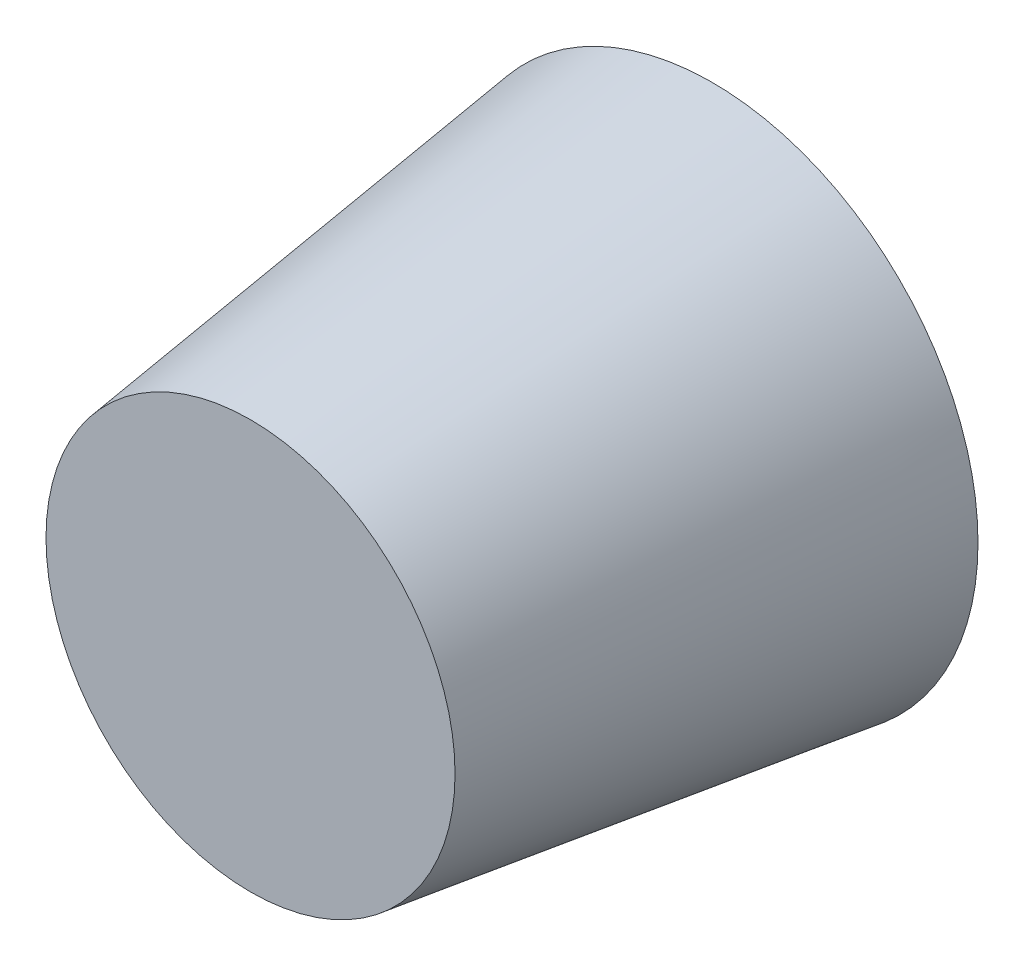
SolidWorks part; units mm, degrees
ref_plane "Front" through (0, 0, 0) normal (0, 0, 1) x (1, 0, 0)
ref_plane "Top" through (0, 0, 0) normal (0, 1, 0) x (1, 0, 0)
ref_plane "Right" through (0, 0, 0) normal (1, 0, 0) x (0, 0, -1)
sketch "草图4" plane through (0, 0, 0) normal (0, 1, 0) x (1, 0, 0)
  line L0 (0, 0) -> (0, 1)
  line L1 (0, 1) -> (14.5, 1)
  line L2 (0, 0) -> (15.5, 0)
  line L5 (19, 35) -> (14.5, 1)
  line L6 (15.5, 0) -> (20.1324, 35)
  line L7 (20.1324, 35) -> (19, 35)
revolve "旋转1" add sketch "草图4" angle 360 about L0
